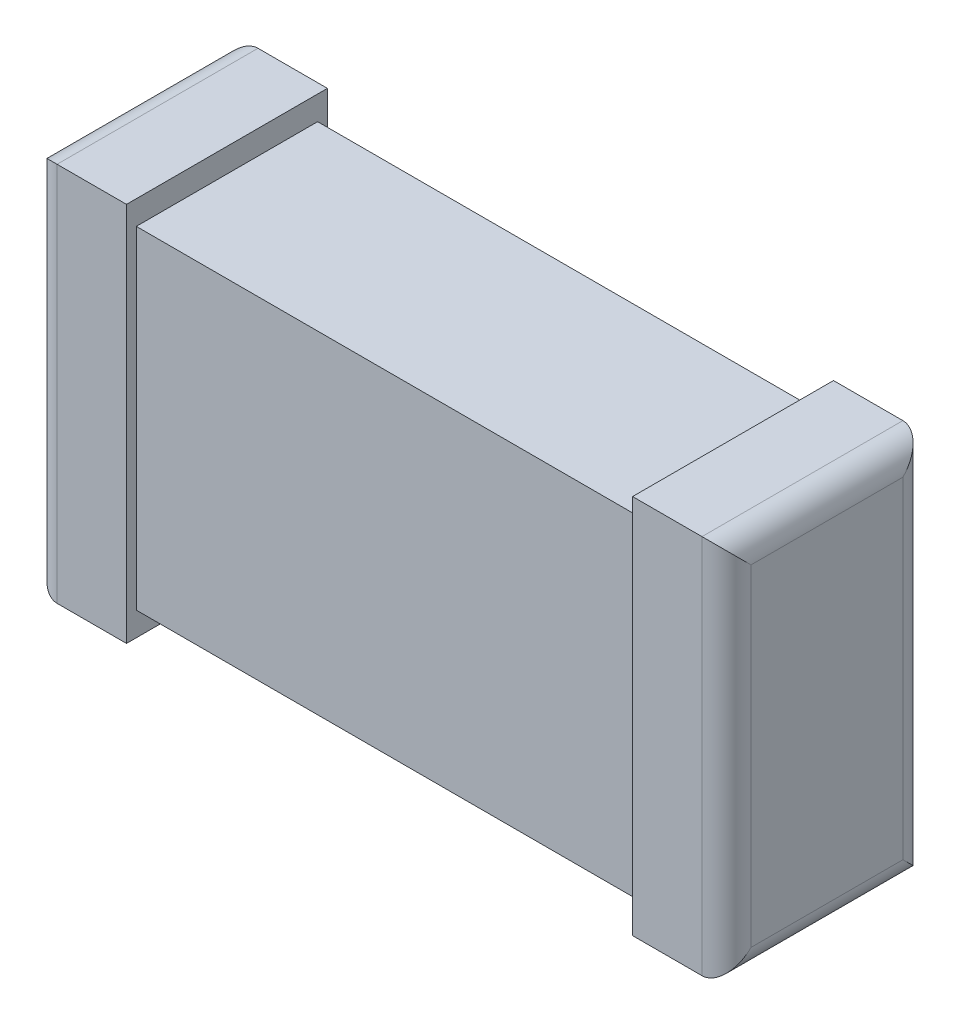
SolidWorks part; units mm, degrees
ref_plane "Plan de face" through (0, 0, 0) normal (0, 0, 1) x (1, 0, 0)
ref_plane "Plan de dessus" through (0, 0, 0) normal (0, 1, 0) x (1, 0, 0)
ref_plane "Plan de droite" through (0, 0, 0) normal (1, 0, 0) x (0, 0, -1)
sketch "Esquisse1" plane through (0, 0, 0) normal (0, 0, 1) x (1, 0, 0)
  line L1 (-3.54, -1.94) -> (3.54, -1.94)
  line L2 (-3.54, -1.94) -> (-3.54, 1.94)
  line L3 (-3.54, 1.94) -> (3.54, 1.94)
  line L4 (3.54, -1.94) -> (3.54, 1.94)
  line L5 (-3.54, -1.94) -> (3.54, 1.94) construction
  line L6 (-3.54, 1.94) -> (3.54, -1.94) construction
  point P0 (0, 0)
  dimension "D1" = 7.08
  dimension "D2" = 3.88
extrude "Boss.-Extru.1" add sketch "Esquisse1" along normal blind 2.05
sketch "Esquisse3" plane through (0, 0, 2.05) normal (0, 0, 1) x (1, 0, 0)
  line L0 (-3.54, 0) -> (0, 0) construction
  line L1 (-3.54, 1.94) -> (-3.54, -1.94) construction
  line L2 (3.54, 1.94) -> (-3.54, 1.94) construction
  line L3 (-2.5818, 2.1845) -> (2.5818, 2.1845)
  line L4 (-2.5818, 2.1845) -> (-2.5818, 1.6955)
  line L5 (-2.5818, 1.6955) -> (2.5818, 1.6955)
  line L6 (2.5818, 2.1845) -> (2.5818, 1.6955)
  line L7 (-2.5818, 2.1845) -> (2.5818, 1.6955) construction
  line L8 (-2.5818, 1.6955) -> (2.5818, 2.1845) construction
  line L9 (-2.5818, -1.6955) -> (2.5818, -1.6955)
  line L10 (2.5818, -2.1845) -> (2.5818, -1.6955)
  line L11 (-2.5818, -2.1845) -> (2.5818, -2.1845)
  line L12 (-2.5818, -2.1845) -> (-2.5818, -1.6955)
  line L13 (-2.5818, -1.6955) -> (2.5818, -2.1845) construction
  line L14 (-2.5818, -2.1845) -> (2.5818, -1.6955) construction
  point P5 (0, 1.94)
  point P16 (0, -1.94)
extrude "Enlèv. mat.-Extru.1" cut sketch "Esquisse3" against normal blind 2.05
sketch "Esquisse4" plane through (0, 0, 2.05) normal (0, 0, 1) x (1, 0, 0)
  line L1 (2.5818, -1.6955) -> (-2.5818, -1.6955)
  line L2 (2.5818, -1.6955) -> (2.5818, 1.6955)
  line L3 (2.5818, 1.6955) -> (-2.5818, 1.6955)
  line L4 (-2.5818, -1.6955) -> (-2.5818, 1.6955)
  line L5 (2.5818, -1.6955) -> (-2.5818, 1.6955) construction
  line L6 (2.5818, 1.6955) -> (-2.5818, -1.6955) construction
  point P0 (0, 0)
extrude "Enlèv. mat.-Extru.2" cut sketch "Esquisse4" against normal blind 0.1
sketch "Esquisse5" plane through (0, 0, 0) normal (0, 0, -1) x (-1, 0, 0)
  line L1 (-2.5818, 1.6955) -> (2.5818, 1.6955)
  line L2 (-2.5818, 1.6955) -> (-2.5818, -1.6955)
  line L3 (-2.5818, -1.6955) -> (2.5818, -1.6955)
  line L4 (2.5818, 1.6955) -> (2.5818, -1.6955)
  line L5 (-2.5818, 1.6955) -> (2.5818, -1.6955) construction
  line L6 (-2.5818, -1.6955) -> (2.5818, 1.6955) construction
  point P0 (0, 0)
extrude "Enlèv. mat.-Extru.3" cut sketch "Esquisse5" against normal blind 0.1
fillet "Congé1" radius 0.25 8 edges at (3.54, -1.94, 1.025) (3.54, 0, 0) (3.54, 0, 2.05) (3.54, 1.94, 1.025) (-3.54, 1.94, 1.025) (-3.54, 0, 0) (-3.54, -1.94, 1.025) (-3.54, 0, 2.05)
